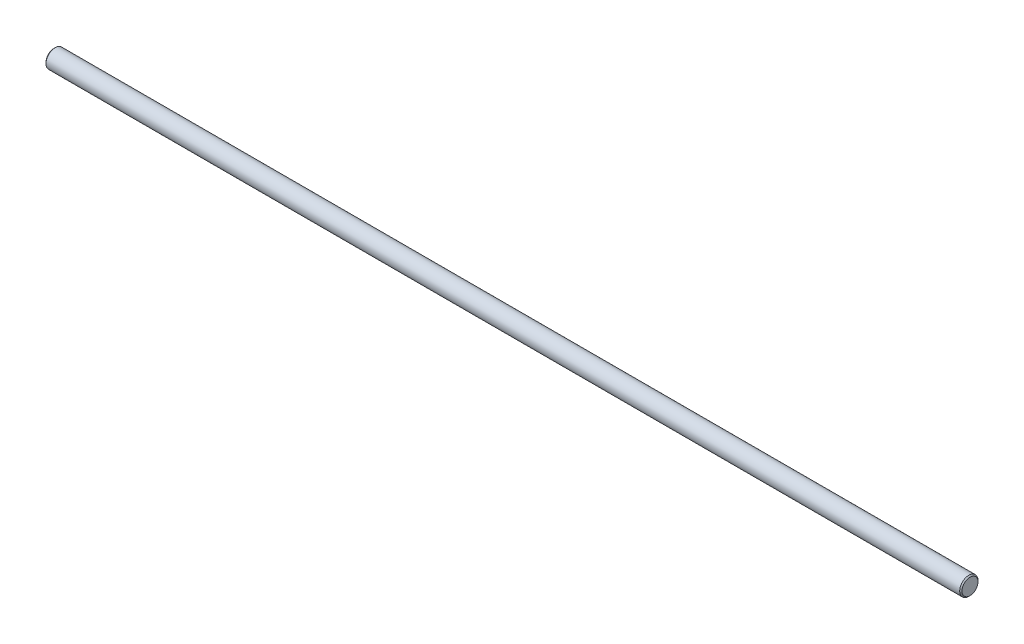
SolidWorks part; units mm, degrees
ref_plane "Front Plane" through (0, 0, 0) normal (0, 0, 1) x (1, 0, 0)
ref_plane "Top Plane" through (0, 0, 0) normal (0, 1, 0) x (1, 0, 0)
ref_plane "Right Plane" through (0, 0, 0) normal (1, 0, 0) x (0, 0, -1)
sketch "Sketch1" plane through (0, 0, 0) normal (1, 0, 0) x (0, 0, -1)
  circle A0 centre (0, 0) radius 4
  dimension "D1" = 8
extrude "Boss-Extrude1" add sketch "Sketch1" along normal blind 400
chamfer "Chamfer1" distance 0.5 angle 45 2 edges at (400, 0, -4) (0, 0, -4)
